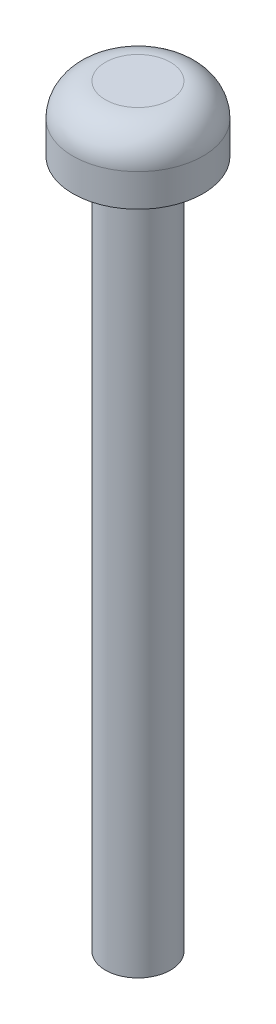
SolidWorks part; units mm, degrees
ref_plane "Front Plane" through (0, 0, 0) normal (0, 0, 1) x (1, 0, 0)
ref_plane "Top Plane" through (0, 0, 0) normal (0, 1, 0) x (1, 0, 0)
ref_plane "Right Plane" through (0, 0, 0) normal (1, 0, 0) x (0, 0, -1)
sketch "Sketch1" plane through (0, 0, 0) normal (0, 1, 0) x (1, 0, 0)
  circle A0 centre (0, 0) radius 3
  dimension "D1" = 6
extrude "Boss-Extrude1" add sketch "Sketch1" along normal blind 3
fillet "Fillet1" radius 1.5 1 edges at (0, 3, 3)
sketch "Sketch2" plane through (0, 0, 0) normal (0, -1, 0) x (1, 0, 0)
  circle A0 centre (0, 0) radius 1.5
  dimension "D1" = 3
extrude "Boss-Extrude2" add sketch "Sketch2" along normal blind 31.75
